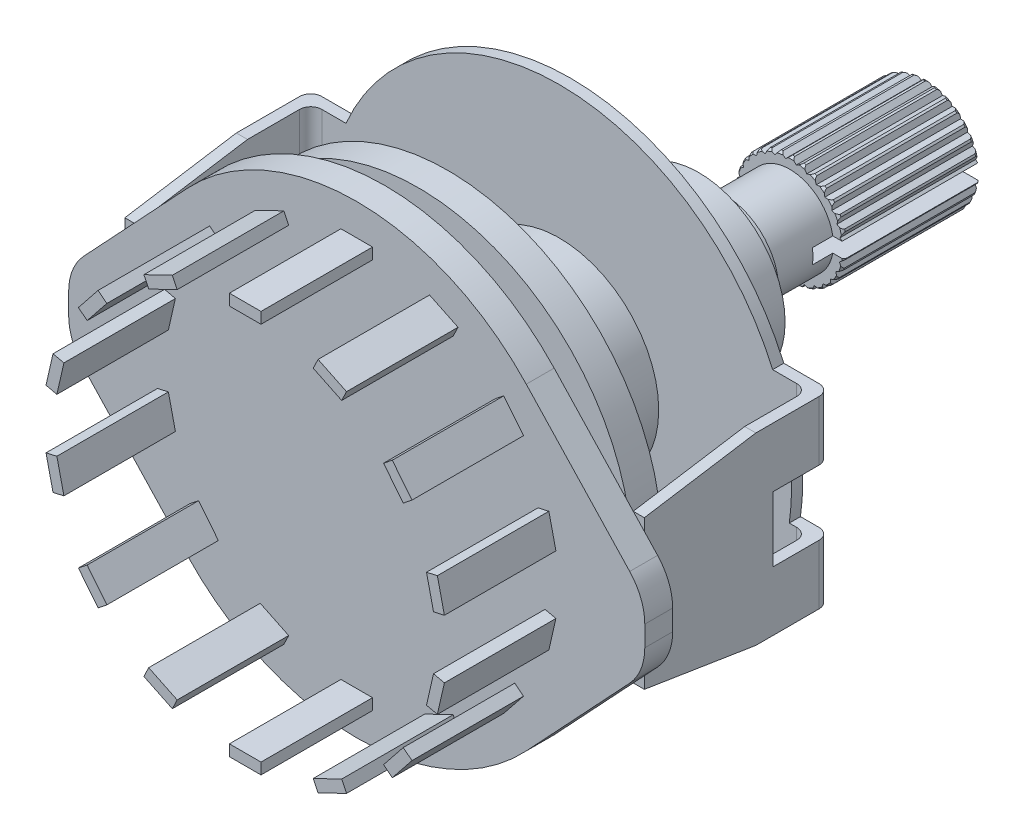
SolidWorks part; units mm, degrees
ref_plane "Front" through (0, 0, 0) normal (0, 0, 1) x (1, 0, 0)
ref_plane "Top" through (0, 0, 0) normal (0, 1, 0) x (1, 0, 0)
ref_plane "Right" through (0, 0, 0) normal (1, 0, 0) x (0, 0, -1)
sketch "Croquis1" plane through (0, 0, 0) normal (0, 0, 1) x (1, 0, 0)
  circle A0 centre (0, 0) radius 2.95
  dimension "D1" = 5.9
extrude "Saliente-Extruir1" add sketch "Croquis1" along normal blind 7.3
sketch "Croquis2" plane through (0, 0, 7.3) normal (0, 0, 1) x (1, 0, 0)
  circle A0 centre (0, 0) radius 2.35
  dimension "D1" = 4.7
extrude "Saliente-Extruir2" add sketch "Croquis2" along normal blind 3.5
sketch "Croquis3" plane through (0, 0, 10.8) normal (0, 0, 1) x (1, 0, 0)
  circle A0 centre (0, 0) radius 2.9
  dimension "D1" = 5.8
extrude "Saliente-Extruir3" add sketch "Croquis3" along normal blind 1.4
sketch "Croquis4" plane through (0, 0, 12.2) normal (0, 0, 1) x (1, 0, 0)
  circle A0 centre (0, 0) radius 4.65
  dimension "D1" = 9.3
extrude "Saliente-Extruir4" add sketch "Croquis4" along normal blind 6
sketch "Croquis5" plane through (0, 0, 18.2) normal (0, 0, 1) x (1, 0, 0)
  circle A0 centre (0, 0) radius 5.35
  dimension "D1" = 10.7
extrude "Saliente-Extruir5" add sketch "Croquis5" along normal blind 0.9
sketch "Croquis6" plane through (0, 0, 19.1) normal (0, 0, 1) x (1, 0, 0)
  line L0 (-5.5, -11.225) -> (5.5, -11.225)
  arc A0 (5.5, -11.225) -> (-5.5, -11.225) centre (0, 0) ccw
  dimension "D1" = 25
  dimension "D2" = 11
extrude "Saliente-Extruir6" add sketch "Croquis6" along normal blind 0.6
sketch "Croquis11" plane through (0, 0, 19.7) normal (0, 0, 1) x (1, 0, 0)
  line L0 (0, 0) -> (-13.7795, 0) construction
  line L1 (-12.3769, 1.75) -> (-13.3769, 1.75)
  line L2 (-11.4781, 4.95) -> (-13.3769, 4.95)
  line L3 (-13.3769, 1.75) -> (-13.3769, 4.95)
  line L4 (-11.4781, -4.95) -> (-13.3769, -4.95)
  line L5 (-13.3769, -1.75) -> (-13.3769, -4.95)
  line L6 (-12.3769, -1.75) -> (-13.3769, -1.75)
  line L8 (-5.5, -11.225) -> (5.5, -11.225)
  arc A0 (5.5, -11.225) -> (-5.5, -11.225) centre (0, 0) ccw construction
  arc A1 (-12.3769, -1.75) -> (-11.4781, -4.95) centre (0, 0) ccw
  arc A2 (5.5, -11.225) -> (-5.5, -11.225) centre (0, 0) ccw
  arc A3 (-11.4781, 4.95) -> (-12.3769, 1.75) centre (0, 0) ccw
  dimension "D1" = 1.75
  dimension "D2" = 3.2
  dimension "D3" = 1
  dimension "D4" = 0
extrude "Saliente-Extruir7" add sketch "Croquis11" against normal up to surface (0.6 mm away) up to face at (5.35, 0, 19.1)
sketch "Croquis12" plane through (-13.3769, 0, 0) normal (-1, 0, 0) x (0, 0, 1)
  line L0 (19.1, 4.95) -> (23.1, 4.95)
  line L1 (19.1, 0) -> (30.3737, 0) construction
  line L2 (19.1, 1.75) -> (19.1, -1.75) construction
  line L3 (29.1, -4) -> (29.1, 4)
  line L4 (23.1, 4.95) -> (29.1, 4)
  line L5 (19.1, 4.95) -> (19.1, 1.75)
  line L6 (19.1, 1.75) -> (22.1865, 1.75)
  line L7 (23.1, -4.95) -> (29.1, -4)
  line L8 (19.1, -1.75) -> (22.1865, -1.75)
  line L9 (19.1, -4.95) -> (19.1, -1.75)
  line L10 (19.1, -4.95) -> (23.1, -4.95)
  line L11 (22.1865, 1.75) -> (22.1865, -1.75)
  point P14 (29.1, 0)
  dimension "D1" = 4
  dimension "D2" = 4
  dimension "D3" = 10
extrude "Saliente-Extruir8" add sketch "Croquis12" along normal blind 0.6
mirror "Simetría1" about plane through (0, 0, 0) normal (1, 0, 0) of "Saliente-Extruir7", "Saliente-Extruir8"
fillet "Redondeo1" radius 0.6 8 edges at (-13.3769, 3.35, 19.7) (-13.3769, -3.35, 19.7) (-13.9769, -3.35, 19.1) (-13.9769, 3.35, 19.1) (13.3769, -3.35, 19.7) (13.3769, 3.35, 19.7) (13.9769, -3.35, 19.1) (13.9769, 3.35, 19.1)
sketch "Croquis13" plane through (0, 0, 19.1) normal (0, 0, -1) x (-1, 0, 0)
  line L0 (0, 0) -> (0, -14.0591) construction
  line L1 (1.5, -11.225) -> (1.5, -11.425)
  line L2 (5.5, -11.225) -> (-5.5, -11.225) construction
  line L3 (-1.5, -11.225) -> (-1.5, -11.425)
  line L4 (-1.5, -11.425) -> (1.5431, -11.425)
  line L5 (1.5, -11.225) -> (-1.5, -11.225)
  line M8 (-5.5, -11.225) -> (5.5, -11.225)
  dimension "D1" = 1.5
  dimension "D2" = 0.2
extrude "Saliente-Extruir9" add sketch "Croquis13" along normal blind 2 from surface at -0.6 separate body contours L0 L3 L4 M8 | L5 L0 L4 L1 starting at face at (0, -0.8872, 19.7)
sketch "Croquis14" plane through (0, 0, 29.1) normal (0, 0, 1) x (1, 0, 0)
  line L0 (13.6769, 4) -> (13.6769, -4) construction
  line L1 (13.9769, 4) -> (13.3769, 4) construction
  line L2 (13.9769, -4) -> (13.3769, -4) construction
  line L3 (13.9769, -4) -> (13.9769, 4) construction
  line L4 (13.3769, 2) -> (13.9769, 2)
  line L5 (13.3769, 2) -> (13.3769, -2)
  line L6 (13.3769, -2) -> (13.9769, -2)
  line L7 (13.9769, 2) -> (13.9769, -2)
  line L8 (13.3769, 2) -> (13.9769, -2) construction
  line L9 (13.3769, -2) -> (13.9769, 2) construction
  point P6 (13.6769, 0)
  dimension "D1" = 4
extrude "Saliente-Extruir10" add sketch "Croquis14" along normal blind 1.5
mirror "Simetría2" about plane through (0, 0, 0) normal (1, 0, 0) of "Saliente-Extruir10"
sketch "Croquis15" plane through (0, 0, 19.7) normal (0, 0, 1) x (1, 0, 0)
  line L0 (0, 0) -> (14.3142, 0) construction
  line L1 (15.5, 0) -> (15.5, 1.7371)
  line L2 (9.1229, 8.5453) -> (15.5, 1.7371)
  line L3 (9.1229, -8.5453) -> (15.5, -1.7371)
  line L4 (15.5, 0) -> (15.5, -1.7371)
  line L5 (0, 12.5) -> (0, -12.5) construction
  line L6 (-9.1229, -8.5453) -> (-15.5, -1.7371)
  line L7 (-15.5, 0) -> (-15.5, -1.7371)
  line L8 (-15.5, 0) -> (-15.5, 1.7371)
  line L9 (-9.1229, 8.5453) -> (-15.5, 1.7371)
  arc A0 (9.1229, 8.5453) -> (-9.1229, 8.5453) centre (0, 0) ccw
  arc A1 (-9.1229, -8.5453) -> (9.1229, -8.5453) centre (0, 0) ccw
  dimension "D3" = 25
extrude "Saliente-Extruir11" add sketch "Croquis15" along normal up to surface (1.5 mm away) from surface at 9.4 up to face at (-13.6769, 0, 30.6) starting at face at (-13.6769, 3, 29.1)
fillet "Redondeo2" radius 3 4 edges at (-15.5, 1.7371, 29.85) (-15.5, -1.7371, 29.85) (15.5, -1.7371, 29.85) (15.5, 1.7371, 29.85)
sketch "Croquis16" plane through (0, 0, 0) normal (0, 0, -1) x (-1, 0, 0)
  line L0 (-0.5158, -6.5996) -> (-0.5158, 2.9046) construction
  line L1 (-0.5158, -6.5996) -> (-0.0153, 2.95) construction
  line L2 (-0.5158, -6.5996) -> (0.4837, 2.9101) construction
  line L3 (-0.0153, 2.95) -> (0.2178, 2.7378)
  line L4 (0.2178, 2.7378) -> (0.4837, 2.9101)
  line L5 (0.7822, 2.6327) -> (1.0782, 2.7459)
  line L6 (0.2247, 2.859) -> (0.23, 2.9537) construction
  line L7 (0.5983, 2.8887) -> (0.7822, 2.6327)
  line L8 (1.3125, 2.4125) -> (1.6255, 2.4617)
  line L9 (1.1859, 2.7012) -> (1.3125, 2.4125)
  line L10 (1.7854, 2.0869) -> (2.1018, 2.07)
  line L11 (1.7216, 2.3956) -> (1.7854, 2.0869)
  line L12 (2.1803, 1.6701) -> (2.4863, 1.5877)
  line L13 (2.182, 1.9853) -> (2.1803, 1.6701)
  line L14 (2.4799, 1.1803) -> (2.7621, 1.0361)
  line L15 (2.5471, 1.4882) -> (2.4799, 1.1803)
  line L16 (2.6711, 0.6389) -> (2.9171, 0.4392)
  line L17 (2.8008, 0.9262) -> (2.6711, 0.6389)
  line L18 (2.7456, 0.0696) -> (2.9447, -0.1769)
  line L19 (2.9322, 0.3236) -> (2.7456, 0.0696)
  line L20 (2.7, -0.5028) -> (2.8436, -0.7853)
  line L21 (2.9354, -0.2931) -> (2.7, -0.5028)
  line L22 (2.5365, -1.0531) -> (2.6182, -1.3593)
  line L23 (2.8103, -0.897) -> (2.5365, -1.0531)
  line L24 (2.2621, -1.5575) -> (2.2783, -1.8739)
  line L25 (2.5624, -1.4617) -> (2.2621, -1.5575)
  line L26 (1.8889, -1.9938) -> (1.8389, -2.3067)
  line L27 (2.2025, -1.9625) -> (1.8889, -1.9938)
  line L28 (1.433, -2.3429) -> (1.3192, -2.6386)
  line L29 (1.7463, -2.3776) -> (1.433, -2.3429)
  line L30 (0.9146, -2.5897) -> (0.7417, -2.8552)
  line L31 (1.2138, -2.6887) -> (0.9146, -2.5897)
  line L32 (0.3562, -2.7232) -> (0.1319, -2.9471)
  line L33 (0.6283, -2.8823) -> (0.3562, -2.7232)
  line L34 (-0.2178, -2.7378) -> (-0.4837, -2.9101)
  line L35 (0.0153, -2.95) -> (-0.2178, -2.7378)
  line L36 (-0.7822, -2.6327) -> (-1.0782, -2.7459)
  line L37 (-0.5983, -2.8887) -> (-0.7822, -2.6327)
  line L38 (-1.3125, -2.4125) -> (-1.6255, -2.4617)
  line L39 (-1.1859, -2.7012) -> (-1.3125, -2.4125)
  line L40 (-1.7854, -2.0869) -> (-2.1018, -2.07)
  line L41 (-1.7216, -2.3956) -> (-1.7854, -2.0869)
  line L42 (-2.1803, -1.6701) -> (-2.4863, -1.5877)
  line L43 (-2.182, -1.9853) -> (-2.1803, -1.6701)
  line L44 (-2.4799, -1.1803) -> (-2.7621, -1.0361)
  line L45 (-2.5471, -1.4882) -> (-2.4799, -1.1803)
  line L46 (-2.6711, -0.6389) -> (-2.9171, -0.4392)
  line L47 (-2.8008, -0.9262) -> (-2.6711, -0.6389)
  line L48 (-2.7456, -0.0696) -> (-2.9447, 0.1769)
  line L49 (-2.9322, -0.3236) -> (-2.7456, -0.0696)
  line L50 (-2.7, 0.5028) -> (-2.8436, 0.7853)
  line L51 (-2.9354, 0.2931) -> (-2.7, 0.5028)
  line L52 (-2.5365, 1.0531) -> (-2.6182, 1.3593)
  line L53 (-2.8103, 0.897) -> (-2.5365, 1.0531)
  line L54 (-2.2621, 1.5575) -> (-2.2783, 1.8739)
  line L55 (-2.5624, 1.4617) -> (-2.2621, 1.5575)
  line L56 (-1.8889, 1.9938) -> (-1.8389, 2.3067)
  line L57 (-2.2025, 1.9625) -> (-1.8889, 1.9938)
  line L58 (-1.433, 2.3429) -> (-1.3192, 2.6386)
  line L59 (-1.7463, 2.3776) -> (-1.433, 2.3429)
  line L60 (-0.9146, 2.5897) -> (-0.7417, 2.8552)
  line L61 (-1.2138, 2.6887) -> (-0.9146, 2.5897)
  line L62 (-0.3562, 2.7232) -> (-0.1319, 2.9471)
  line L63 (-0.6283, 2.8823) -> (-0.3562, 2.7232)
  circle A0 centre (0, 0) radius 2.95 construction
  circle A2 centre (0, 0) radius 2.95
  arc A3 (0.4837, 2.9101) -> (-0.0153, 2.95) centre (0, 0) ccw
  arc A4 (1.0782, 2.7459) -> (0.5983, 2.8887) centre (0, 0) ccw
  arc A5 (-0.1319, 2.9471) -> (-0.6283, 2.8823) centre (0, 0) ccw
  arc A6 (-0.7417, 2.8552) -> (-1.2138, 2.6887) centre (0, 0) ccw
  arc A7 (-1.3192, 2.6386) -> (-1.7463, 2.3776) centre (0, 0) ccw
  arc A8 (-1.8389, 2.3067) -> (-2.2025, 1.9625) centre (0, 0) ccw
  arc A9 (-2.2783, 1.8739) -> (-2.5624, 1.4617) centre (0, 0) ccw
  arc A10 (-2.6182, 1.3593) -> (-2.8103, 0.897) centre (0, 0) ccw
  arc A11 (-2.8436, 0.7853) -> (-2.9354, 0.2931) centre (0, 0) ccw
  arc A12 (-2.9447, 0.1769) -> (-2.9322, -0.3236) centre (0, 0) ccw
  arc A13 (-2.9171, -0.4392) -> (-2.8008, -0.9262) centre (0, 0) ccw
  arc A14 (-2.7621, -1.0361) -> (-2.5471, -1.4882) centre (0, 0) ccw
  arc A15 (-2.4863, -1.5877) -> (-2.182, -1.9853) centre (0, 0) ccw
  arc A16 (-2.1018, -2.07) -> (-1.7216, -2.3956) centre (0, 0) ccw
  arc A17 (-1.6255, -2.4617) -> (-1.1859, -2.7012) centre (0, 0) ccw
  arc A18 (-1.0782, -2.7459) -> (-0.5983, -2.8887) centre (0, 0) ccw
  arc A19 (-0.4837, -2.9101) -> (0.0153, -2.95) centre (0, 0) ccw
  arc A20 (0.1319, -2.9471) -> (0.6283, -2.8823) centre (0, 0) ccw
  arc A21 (0.7417, -2.8552) -> (1.2138, -2.6887) centre (0, 0) ccw
  arc A22 (1.3192, -2.6386) -> (1.7463, -2.3776) centre (0, 0) ccw
  arc A23 (1.8389, -2.3067) -> (2.2025, -1.9625) centre (0, 0) ccw
  arc A24 (2.2783, -1.8739) -> (2.5624, -1.4617) centre (0, 0) ccw
  arc A25 (2.6182, -1.3593) -> (2.8103, -0.897) centre (0, 0) ccw
  arc A26 (2.8436, -0.7853) -> (2.9354, -0.2931) centre (0, 0) ccw
  arc A27 (2.9447, -0.1769) -> (2.9322, 0.3236) centre (0, 0) ccw
  arc A28 (2.9171, 0.4392) -> (2.8008, 0.9262) centre (0, 0) ccw
  arc A29 (2.7621, 1.0361) -> (2.5471, 1.4882) centre (0, 0) ccw
  arc A30 (2.4863, 1.5877) -> (2.182, 1.9853) centre (0, 0) ccw
  arc A31 (2.1018, 2.07) -> (1.7216, 2.3956) centre (0, 0) ccw
  arc A32 (1.6255, 2.4617) -> (1.1859, 2.7012) centre (0, 0) ccw
  point P104 (0, 0)
  dimension "D2" = 3
  dimension "D3" = 3
  dimension "D1" = 0
  dimension "D4" = 30
extrude "Cortar-Extruir1" cut sketch "Croquis16" against normal up to next (7.3 mm away)
sketch "Croquis17" plane through (0, 0, 0) normal (0, 0, -1) x (-1, 0, 0)
  line L1 (-3.2428, 0.4) -> (3.2428, 0.4)
  line L2 (-3.2428, 0.4) -> (-3.2428, -0.4)
  line L3 (-3.2428, -0.4) -> (3.2428, -0.4)
  line L4 (3.2428, 0.4) -> (3.2428, -0.4)
  line L5 (-3.2428, 0.4) -> (3.2428, -0.4) construction
  line L6 (-3.2428, -0.4) -> (3.2428, 0.4) construction
  point P0 (0, 0)
  dimension "D1" = 0.8
extrude "Cortar-Extruir2" cut sketch "Croquis17" against normal blind 8.4
sketch "Croquis18" plane through (0, 0, 0) normal (0, 1, 0) x (1, 0, 0)
  line L0 (2.7827, 0.0429) -> (2.9777, 0.0429)
  line L1 (2.9777, 0.0429) -> (2.9777, -0.1492)
  line L2 (2.9777, -0.1492) -> (2.9523, -0.1492)
  line L3 (0, 0) -> (0, 1.9204) construction
  line L4 (0, 0) -> (0, -7.3) construction
  line L5 (-2.3157, -7.3) -> (2.3157, -7.3) construction
  line L6 (0, -3.65) -> (-7.0882, -3.65) construction
  line L7 (2.9777, -7.3429) -> (2.9777, -7.1508)
  line L8 (2.7827, -7.3429) -> (2.9777, -7.3429)
  line L9 (2.9777, -7.1508) -> (2.9523, -7.1508)
  spline S0 degree 2 poles (2.7827, 0.0429) (2.9125, -0.0134) (2.9523, -0.1492) knots 0 0 0 1 1 1
  spline S1 degree 2 poles (2.7827, -7.3429) (2.9125, -7.2866) (2.9523, -7.1508) knots 0 0 0 1 1 1
revolve "Cortar-Revolución1" cut sketch "Croquis18" angle 360 about L3
sketch "Croquis19" plane through (0, 0, 30.6) normal (0, 0, 1) x (1, 0, 0)
  line L0 (0, 0) -> (0, 10.5) construction
  line L1 (3.9201, 10.0993) -> (3.6598, 9.5587)
  line L2 (-0.85, 10.8) -> (0.85, 10.8)
  line L3 (-0.85, 10.8) -> (-0.85, 10.2)
  line L4 (-0.85, 10.2) -> (0.85, 10.2)
  line L5 (0.85, 10.8) -> (0.85, 10.2)
  line L6 (-0.85, 10.8) -> (0.85, 10.2) construction
  line L7 (-0.85, 10.2) -> (0.85, 10.8) construction
  line L8 (3.9201, 10.0993) -> (5.4518, 9.3617)
  line L9 (5.4518, 9.3617) -> (5.1914, 8.8211)
  line L10 (3.6598, 9.5587) -> (5.1914, 8.8211)
  line L11 (7.9138, 7.3982) -> (7.4447, 7.0242)
  line L12 (7.9138, 7.3982) -> (8.9737, 6.0691)
  line L13 (8.9737, 6.0691) -> (8.5046, 5.695)
  line L14 (7.4447, 7.0242) -> (8.5046, 5.695)
  line L15 (10.3401, 3.2319) -> (9.7551, 3.0984)
  line L16 (10.3401, 3.2319) -> (10.7184, 1.5745)
  line L17 (10.7184, 1.5745) -> (10.1334, 1.441)
  line L18 (9.7551, 3.0984) -> (10.1334, 1.441)
  line L19 (10.7184, -1.5745) -> (10.1334, -1.441)
  line L20 (10.7184, -1.5745) -> (10.3401, -3.2319)
  line L21 (10.3401, -3.2319) -> (9.7551, -3.0984)
  line L22 (10.1334, -1.441) -> (9.7551, -3.0984)
  line L23 (8.9737, -6.0691) -> (8.5046, -5.695)
  line L24 (8.9737, -6.0691) -> (7.9138, -7.3982)
  line L25 (7.9138, -7.3982) -> (7.4447, -7.0242)
  line L26 (8.5046, -5.695) -> (7.4447, -7.0242)
  line L27 (5.4518, -9.3617) -> (5.1914, -8.8211)
  line L28 (5.4518, -9.3617) -> (3.9201, -10.0993)
  line L29 (3.9201, -10.0993) -> (3.6598, -9.5587)
  line L30 (5.1914, -8.8211) -> (3.6598, -9.5587)
  line L31 (0.85, -10.8) -> (0.85, -10.2)
  line L32 (0.85, -10.8) -> (-0.85, -10.8)
  line L33 (-0.85, -10.8) -> (-0.85, -10.2)
  line L34 (0.85, -10.2) -> (-0.85, -10.2)
  line L35 (-3.9201, -10.0993) -> (-3.6598, -9.5587)
  line L36 (-3.9201, -10.0993) -> (-5.4518, -9.3617)
  line L37 (-5.4518, -9.3617) -> (-5.1914, -8.8211)
  line L38 (-3.6598, -9.5587) -> (-5.1914, -8.8211)
  line L39 (-7.9138, -7.3982) -> (-7.4447, -7.0242)
  line L40 (-7.9138, -7.3982) -> (-8.9737, -6.0691)
  line L41 (-8.9737, -6.0691) -> (-8.5046, -5.695)
  line L42 (-7.4447, -7.0242) -> (-8.5046, -5.695)
  line L43 (-10.3401, -3.2319) -> (-9.7551, -3.0984)
  line L44 (-10.3401, -3.2319) -> (-10.7184, -1.5745)
  line L45 (-10.7184, -1.5745) -> (-10.1334, -1.441)
  line L46 (-9.7551, -3.0984) -> (-10.1334, -1.441)
  line L47 (-10.7184, 1.5745) -> (-10.1334, 1.441)
  line L48 (-10.7184, 1.5745) -> (-10.3401, 3.2319)
  line L49 (-10.3401, 3.2319) -> (-9.7551, 3.0984)
  line L50 (-10.1334, 1.441) -> (-9.7551, 3.0984)
  line L51 (-8.9737, 6.0691) -> (-8.5046, 5.695)
  line L52 (-8.9737, 6.0691) -> (-7.9138, 7.3982)
  line L53 (-7.9138, 7.3982) -> (-7.4447, 7.0242)
  line L54 (-8.5046, 5.695) -> (-7.4447, 7.0242)
  line L55 (-5.4518, 9.3617) -> (-5.1914, 8.8211)
  line L56 (-5.4518, 9.3617) -> (-3.9201, 10.0993)
  line L57 (-3.9201, 10.0993) -> (-3.6598, 9.5587)
  line L58 (-5.1914, 8.8211) -> (-3.6598, 9.5587)
  circle A0 centre (0, 0) radius 10.5 construction
  point P63 (0, 0)
  dimension "D1" = 21
  dimension "D2" = 1.7
  dimension "D3" = 0.6
  dimension "D4" = 14
extrude "Saliente-Extruir12" add sketch "Croquis19" along normal blind 6
sketch "Croquis20" plane through (0, 0, 19.7) normal (0, 0, 1) x (1, 0, 0)
  circle A0 centre (0, 0) radius 5.35
extrude "Saliente-Extruir13" add sketch "Croquis20" along normal blind 6
sketch "Croquis21" plane through (0, 0, 25.7) normal (0, 0, 1) x (1, 0, 0)
  circle A1 centre (0, 0) radius 11.5
  dimension "D1" = 23
extrude "Saliente-Extruir14" add sketch "Croquis21" along normal blind 1.6
